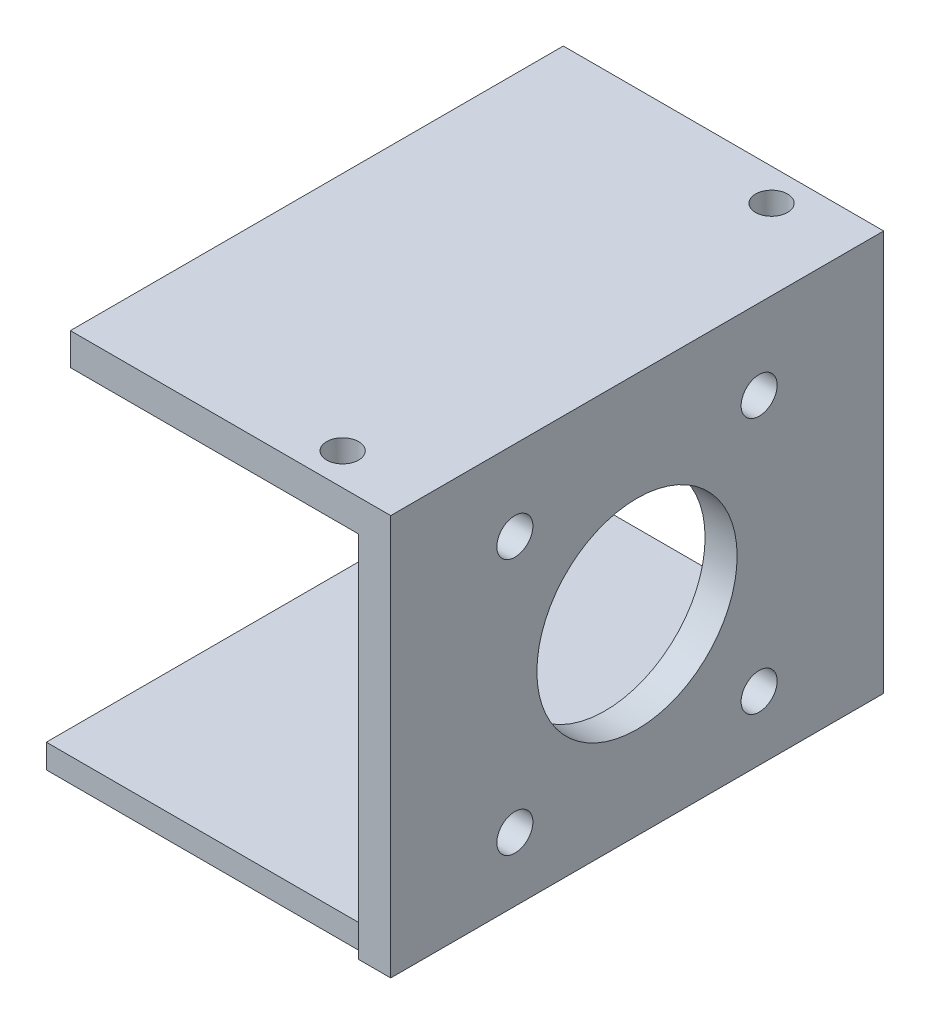
SolidWorks part; units mm, degrees
ref_plane "Alzado" through (0, 0, 0) normal (0, 0, 1) x (1, 0, 0)
ref_plane "Planta" through (0, 0, 0) normal (0, 1, 0) x (1, 0, 0)
ref_plane "Vista lateral" through (0, 0, 0) normal (1, 0, 0) x (0, 0, -1)
sketch "Croquis1" plane through (0, 0, 0) normal (0, 1, 0) x (1, 0, 0)
  line L0 (0, 20.5) -> (0, -21)
  line L1 (40, -21) -> (0, -21)
  line L2 (40, -21) -> (40, 20.5)
  line L3 (40, 20.5) -> (0, 20.5)
  line L5 (40, -21) -> (0, 0) construction
  line L6 (40, 20.5) -> (0, 0) construction
  line L8 (40, 20.5) -> (40, -21)
  circle A1 centre (33.75, 14.25) radius 2.5
  circle A3 centre (33.75, -14.75) radius 2.5
  point P0 (0, 0)
  dimension "D3" = 5
  dimension "D4" = 40
  dimension "D6" = 5
  dimension "D2" = 29
  dimension "D7" = 6.25
  dimension "D8" = 6.25
  dimension "D13" = 6.25
  dimension "D14" = 6.25
extrude "Saliente-Extruir1" add sketch "Croquis1" along normal blind 3
sketch "Croquis2" plane through (0, 0, 0) normal (0, 1, 0) x (1, 0, 0)
  line L1 (40, 20.5) -> (44, 20.5)
  line L2 (40, 20.5) -> (40, -21)
  line L3 (40, -21) -> (44, -21)
  line L4 (44, 20.5) -> (44, -21)
  dimension "D1" = 4
extrude "Saliente-Extruir2" add sketch "Croquis2" along normal blind 45
sketch "Croquis3" plane through (0, 0, 0) normal (1, 0, 0) x (0, 0, -1)
  line L0 (-21, 3) -> (20.5, 3) construction
  line L1 (-21, 45) -> (-21, 0) construction
  line L2 (20.5, 45) -> (20.5, 0) construction
  line L4 (-21, 45) -> (20.5, 45) construction
  circle A0 centre (-0.25, 24) radius 12.5
  circle A1 centre (15, 40) radius 2.25
  circle A2 centre (-15.5, 40) radius 2.25
  circle A3 centre (-15.5, 8) radius 2.25
  circle A4 centre (15, 8) radius 2.25
  point P14 (-0.25, 45)
  dimension "D1" = 25
  dimension "D5" = 4.5
  dimension "D6" = 4.5
  dimension "D7" = 4.5
  dimension "D8" = 4.5
  dimension "D2" = 3
  dimension "D3" = 21
  dimension "D4" = 21
  dimension "D9" = 5.5
  dimension "D10" = 5.5
  dimension "D11" = 5.5
  dimension "D12" = 5.5
  dimension "D13" = 5
  dimension "D14" = 5
  dimension "D15" = 5
  dimension "D16" = 5
extrude "Cortar-Extruir1" cut sketch "Croquis3" against normal up to surface (4 mm away) from surface at 44 up to face at (40, 24, 0.25) starting at face at (44, 22.5, 0.25)
sketch "Croquis5" plane through (0, 0, 0) normal (1, 0, 0) x (0, 0, -1)
  line L0 (-21, 0) -> (-31, 0)
  line L3 (20.5, 0) -> (-21, 0) construction
  line L4 (20.5, 0) -> (-21, 0) construction
  line L5 (-31, 0) -> (-31, 46)
  line L6 (-21, 45) -> (20.5, 45) construction
  line L7 (20.5, 0) -> (30.5, 0)
  line L8 (-31, 46) -> (30.5491, 46)
  line L10 (30.5491, 46) -> (30.5, 0)
  line L11 (-21, 0) -> (-21, 45)
  line L12 (-21, 45) -> (20.5, 45)
  line L13 (20.5, 45) -> (20.5, 0)
  dimension "D1" = 1
  dimension "D2" = 10
  dimension "D3" = 1
  dimension "D4" = 0
  dimension "D5" = 10
  dimension "D6" = 46
extrude "Saliente-Extruir4" add sketch "Croquis5" against normal up to surface (4 mm away) from vertex
sketch "Croquis6" plane through (0, 0, 0) normal (0, 1, 0) x (1, 0, 0)
  line L0 (0, 20.5) -> (0, 30)
  line L1 (0, 30) -> (40, 30)
  line L2 (40, -31) -> (40, 30.5491) construction
  line L3 (40, 30) -> (40, 20.5)
  line L4 (40, 20.5) -> (0, 20.5) construction
  line L5 (40, 20.5) -> (0, 20.5)
  line L6 (0, -21) -> (0, -30)
  line L7 (0, -30) -> (40, -30)
  line L8 (40, -30) -> (40, -21)
  line L9 (40, -21) -> (0, -21)
extrude "Saliente-Extruir5" add sketch "Croquis6" along normal up to surface (3 mm away) up to face at (33.75, 3, 17.25)
sketch "Croquis7" plane through (0, 0, 0) normal (0, 1, 0) x (1, 0, 0)
  line L0 (40, -31) -> (44, -31) construction
  line L1 (44, 30.5491) -> (4, 30.5491)
  line L2 (44, 30.5491) -> (44, -31)
  line L3 (44, -31) -> (4, -31)
  line L4 (4, 30.5491) -> (4, -31)
  circle A0 centre (34, 26.5491) radius 2
  circle A1 centre (34, -27) radius 2
  dimension "D3" = 4
  dimension "D4" = 4
  dimension "D1" = 0
  dimension "D2" = 40
  dimension "D5" = 4
  dimension "D6" = 4
  dimension "D7" = 30
  dimension "D8" = 30
extrude "Saliente-Extruir6" add sketch "Croquis7" along normal blind 4 from vertex at 46
